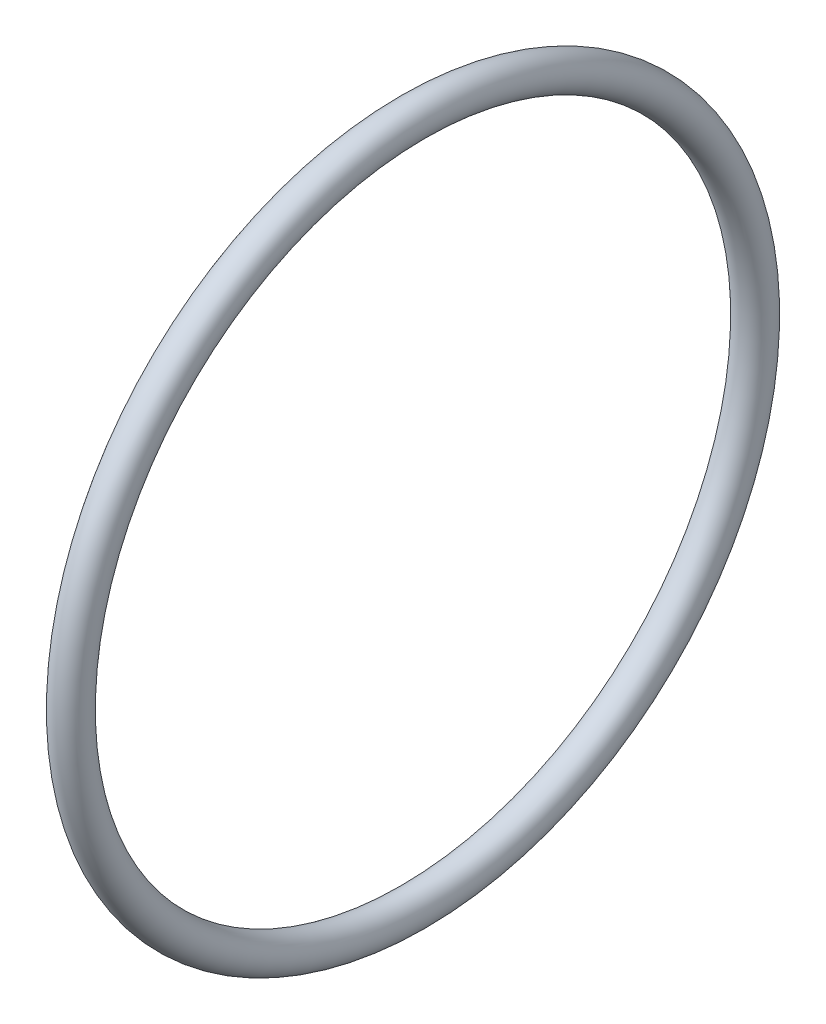
SolidWorks part; units mm, degrees
material "BUTYL"
ref_plane "Front Plane" through (0, 0, 0) normal (0, 0, 1) x (1, 0, 0)
ref_plane "Top Plane" through (0, 0, 0) normal (0, 1, 0) x (1, 0, 0)
ref_plane "Right Plane" through (0, 0, 0) normal (1, 0, 0) x (0, 0, -1)
sketch "Sketch1" plane through (0, 0, 0) normal (0, 0, 1) x (1, 0, 0)
  line L0 (-22.86, 1432.7873) -> (-10.16, 1432.7873) construction
  line L1 (-22.86, 1445.3349) -> (-22.86, 1420.2397) construction
  line L2 (-10.16, 1445.3857) -> (-10.16, 1420.1889) construction
  circle A3 centre (-16.51, 1445.3349) radius 0.635
  circle A4 centre (-16.51, 1445.3349) radius 0.635
  dimension "D2" = 0
revolve "Revolve1" add sketch "Sketch1" angle 360 about L0
